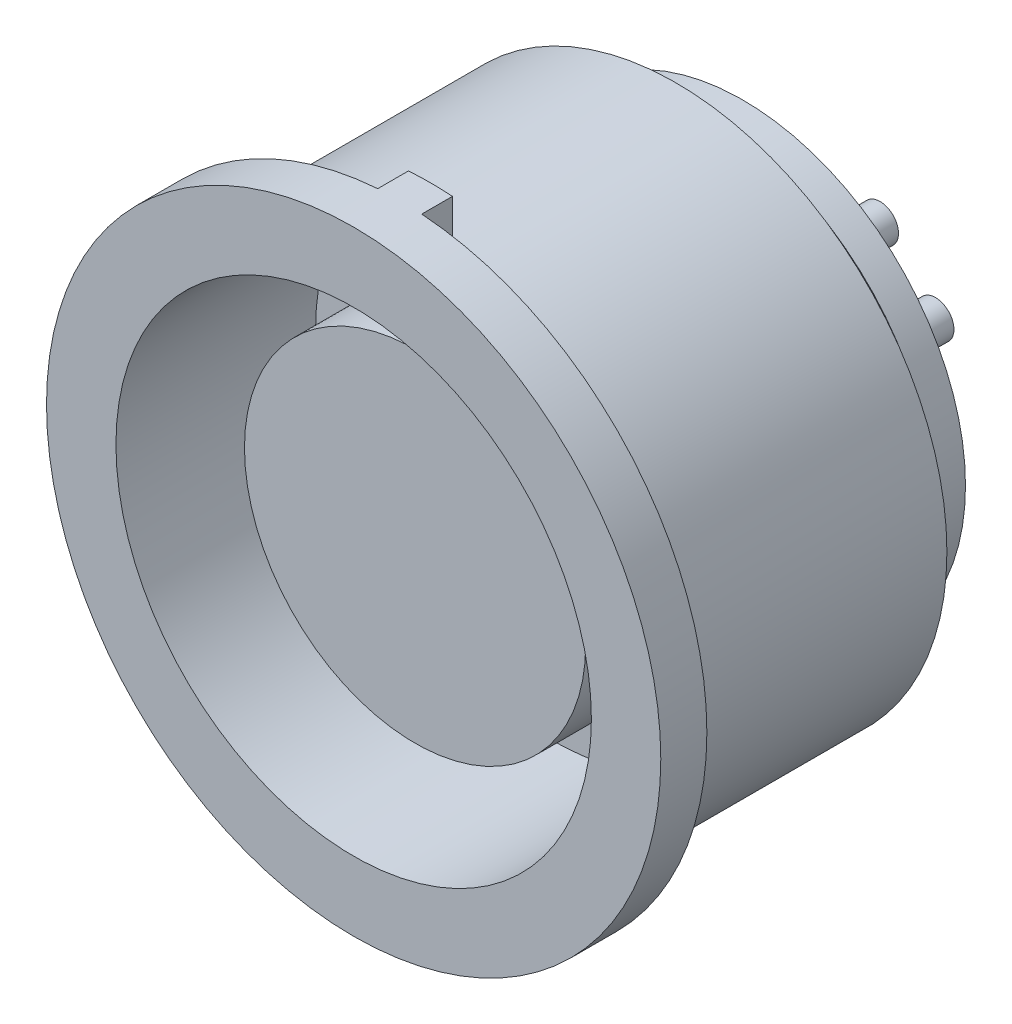
SolidWorks part; units mm, degrees
ref_plane "Front Plane" through (0, 0, 0) normal (0, 0, 1) x (1, 0, 0)
ref_plane "Top Plane" through (0, 0, 0) normal (0, 1, 0) x (1, 0, 0)
ref_plane "Right Plane" through (0, 0, 0) normal (1, 0, 0) x (0, 0, -1)
sketch "Sketch2" plane through (0, 0, 0) normal (1, 0, 0) x (0, 0, -1)
  line L0 (0, 8.815) -> (0, 10)
  line L1 (0, 10) -> (-1.5, 10)
  line L2 (-1.5, 10) -> (-1.5, 7.74)
  line L3 (-1.5, 7.74) -> (5, 7.74)
  line L4 (5, 7.74) -> (5, 5.555)
  line L5 (5, 5.555) -> (0.5, 5.555)
  line L6 (0.5, 5.555) -> (0.5, 0)
  line L7 (0, 8.815) -> (9, 8.815)
  line L8 (9, 8.815) -> (10.1308, 7.25)
  line L9 (10.1308, 7.25) -> (11.17, 7.25)
  line L10 (11.17, 7.25) -> (11.17, 0)
  line L11 (11.17, 0) -> (0.5, 0)
  line L12 (-11.3571, 0) -> (35.3571, 0) construction
  point P15 (-0.5611, 7.9286)
  point P16 (10.2645, 7.25)
  point P17 (10.1308, 7.25)
  dimension "D1" = 20
  dimension "D2" = 2.26
  dimension "D3" = 17.63
  dimension "D4" = 14.5
  dimension "D5" = 9
  dimension "D6" = 12.67
  dimension "D7" = 1.5
  dimension "D8" = 6.5
  dimension "D9" = 11.11
  dimension "D10" = 2
revolve "Revolve1" add sketch "Sketch2" angle 360 about L12
sketch "Sketch3" plane through (0, 0, -11.17) normal (0, 0, -1) x (-1, 0, 0)
  circle A0 centre (1.714, 3.7737) radius 0.6
  circle A1 centre (1.714, 1.9686) radius 0.6
  circle A2 centre (3.5212, 1.9686) radius 0.6
  point P6 (1.8114, 1.9988)
  point P7 (0, 0)
  point P8 (0, 0)
  point P9 (1.714, 3.7737)
  point P10 (3.5212, 1.9686)
  dimension "D1" = 1.2
extrude "Boss-Extrude1" add sketch "Sketch3" along normal blind 2.5
pattern_circular "CirPattern1" count 4 over 360 about axis through (0, 0, 0) along (0, 0, 1) of "Boss-Extrude1"
sketch "Sketch5" plane through (0, 0, 0) normal (0, 0, -1) x (-1, 0, 0)
  line L0 (-0.7167, 9.9743) -> (-0.7167, 8.7858)
  line L1 (0.7167, 9.9743) -> (0.7167, 8.7858)
  line L2 (0, 0) -> (0, 10.7712) construction
  circle A0 centre (0, 0) radius 10 construction
  circle A1 centre (0, 0) radius 8.815 construction
  circle A2 centre (0, 0) radius 8.815 construction
  arc A3 (0.7167, 8.7858) -> (-0.7167, 8.7858) centre (0, 0) ccw
  arc A4 (0.7167, 9.9743) -> (-0.7167, 9.9743) centre (0, 0) ccw
  point P14 (0, 10.7712)
extrude "Boss-Extrude2" add sketch "Sketch5" along normal blind 1
